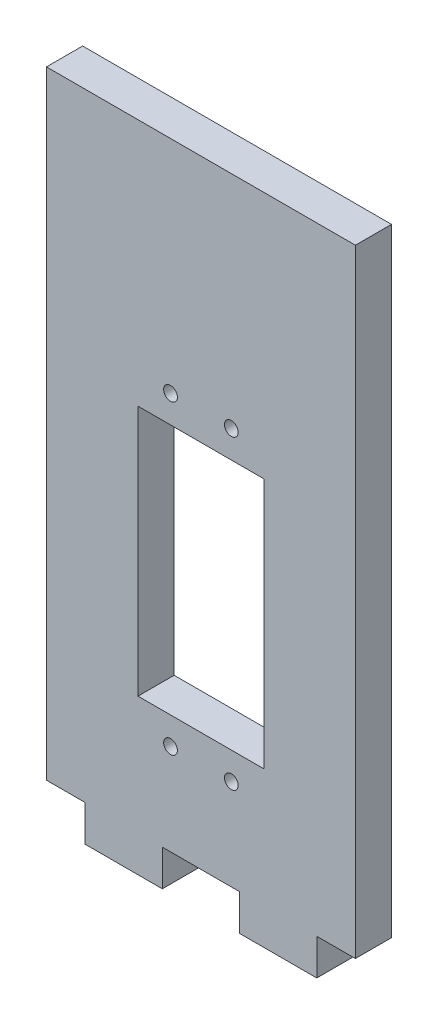
SolidWorks part; units mm, degrees
ref_plane "Front Plane" through (0, 0, 0) normal (0, 0, 1) x (1, 0, 0)
ref_plane "Top Plane" through (0, 0, 0) normal (0, 1, 0) x (1, 0, 0)
ref_plane "Right Plane" through (0, 0, 0) normal (1, 0, 0) x (0, 0, -1)
sketch "Sketch1" plane through (0, 0, 0) normal (0, 0, 1) x (1, 0, 0)
  line L0 (6.35, 0) -> (6.35, -5.9436)
  line L1 (0, 0) -> (6.35, 0)
  line L2 (0, 0) -> (0, 101.6)
  line L3 (0, 101.6) -> (50.8, 101.6)
  line L4 (50.8, 0) -> (50.8, 101.6)
  line L5 (6.35, -5.9436) -> (19.05, -5.9436)
  line L6 (19.05, -5.9436) -> (19.05, 0)
  line L7 (19.05, 0) -> (31.75, 0)
  line L8 (25.4, 101.6) -> (25.4, -5.9436) construction
  line L9 (12.7, -5.9436) -> (12.7, 0) construction
  line L10 (31.75, -5.9436) -> (31.75, 0)
  line L11 (44.45, -5.9436) -> (31.75, -5.9436)
  line L12 (44.45, 0) -> (44.45, -5.9436)
  line L13 (44.45, 0) -> (50.8, 0)
  dimension "D1" = 101.6
  dimension "D2" = 50.8
  dimension "D3" = 5.9436
  dimension "D4" = 12.7
  dimension "D5" = 12.7
extrude "Boss-Extrude1" add sketch "Sketch1" along normal blind 5.9436
sketch "Sketch2" plane through (0, 0, 5.9436) normal (0, 0, 1) x (1, 0, 0)
  line L0 (25.4, 101.6) -> (25.4, 0) construction
  line L1 (50.8, 101.6) -> (0, 101.6) construction
  line L2 (15.05, 21.5) -> (15.05, 19.5) construction
  line L4 (15.05, 60.8) -> (35.75, 60.8)
  line L5 (15.05, 60.8) -> (15.05, 19.5)
  line L6 (15.05, 19.5) -> (35.75, 19.5)
  line L7 (35.75, 60.8) -> (35.75, 19.5)
  circle A1 centre (20.4, 65.3) radius 1.1303
  circle A2 centre (30.4, 65.3) radius 1.1303
  circle A3 centre (20.4, 15) radius 1.1303
  circle A4 centre (30.4, 15) radius 1.1303
  dimension "D1" = 2.2606
extrude "Cut-Extrude1" cut sketch "Sketch2" against normal through all
